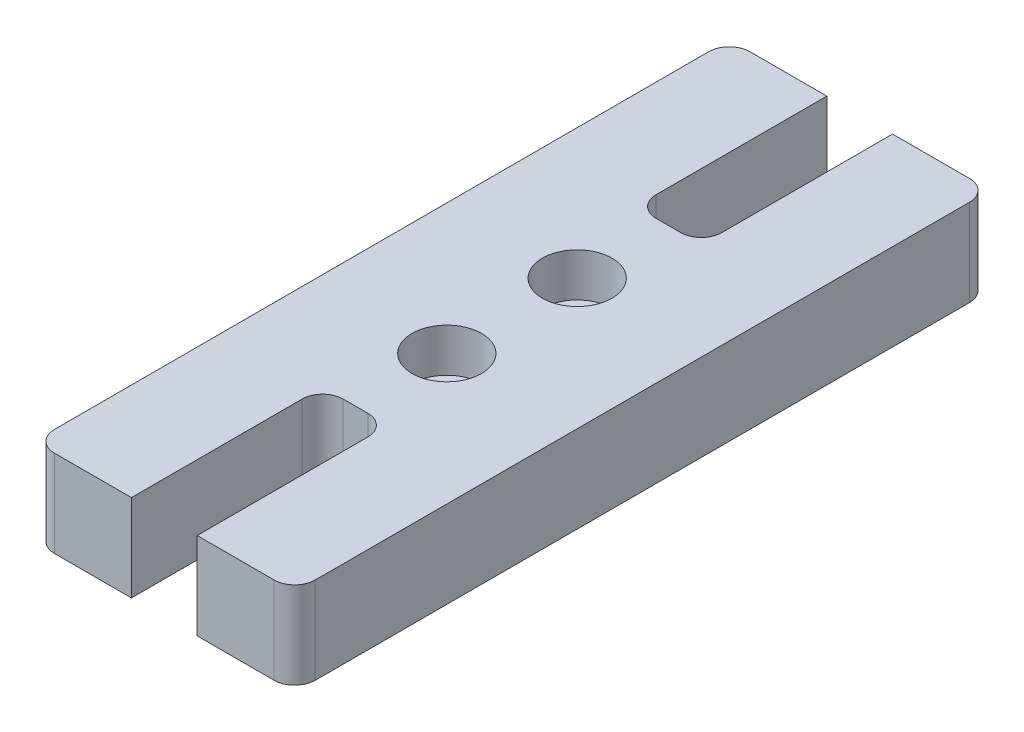
SolidWorks part; units mm, degrees
ref_plane "Front Plane" through (0, 0, 0) normal (0, 0, 1) x (1, 0, 0)
ref_plane "Top Plane" through (0, 0, 0) normal (0, 1, 0) x (1, 0, 0)
ref_plane "Right Plane" through (0, 0, 0) normal (1, 0, 0) x (0, 0, -1)
sketch "Sketch1" plane through (0, 0, 0) normal (0, 1, 0) x (1, 0, 0)
  line L1 (-9.525, -25.4) -> (9.525, -25.4)
  line L2 (-9.525, -25.4) -> (-9.525, 25.4)
  line L3 (-9.525, 25.4) -> (9.525, 25.4)
  line L4 (9.525, -25.4) -> (9.525, 25.4)
  line L5 (-9.525, -25.4) -> (9.525, 25.4) construction
  line L6 (-9.525, 25.4) -> (9.525, -25.4) construction
  point P0 (0, 0)
  dimension "D1" = 50.8
  dimension "D2" = 19.05
extrude "Boss-Extrude1" add sketch "Sketch1" along normal blind 6.35
sketch "Sketch2" plane through (0, 6.35, 0) normal (0, 1, 0) x (1, 0, 0)
  circle A0 centre (0, 4.7625) radius 1.7272
  dimension "D1" = 4.7625
  dimension "D2" = 3.4544
extrude "Cut-Extrude1" cut sketch "Sketch2" against normal through all and the other way through all
sketch "Sketch3" plane through (0, 6.35, 0) normal (0, 1, 0) x (1, 0, 0)
  circle A0 centre (0, 4.7625) radius 2.54
  dimension "D1" = 5.08
extrude "Cut-Extrude2" cut sketch "Sketch3" against normal blind 3.175
sketch "Sketch4" plane through (0, 6.35, 0) normal (0, 1, 0) x (1, 0, 0)
  line L0 (9.525, 25.4) -> (-9.525, 25.4) construction
  line L1 (-2.4003, 11.43) -> (2.4003, 11.43)
  line L2 (-2.4003, 11.43) -> (-2.4003, 25.4)
  line L3 (-2.4003, 25.4) -> (2.4003, 25.4)
  line L4 (2.4003, 11.43) -> (2.4003, 25.4)
  line L5 (-2.4003, 11.43) -> (2.4003, 25.4) construction
  line L6 (-2.4003, 25.4) -> (2.4003, 11.43) construction
  point P0 (0, 18.415)
  dimension "D1" = 4.8006
  dimension "D2" = 13.97
extrude "Cut-Extrude3" cut sketch "Sketch4" against normal through all
mirror "Mirror1" about plane through (0, 0, 0) normal (0, 0, 1) of "Cut-Extrude1", "Cut-Extrude2", "Cut-Extrude3"
fillet "Fillet2" radius 1.5 8 edges at (9.525, 3.175, 25.4) (-9.525, 3.175, 25.4) (2.4003, 3.175, 11.43) (-2.4003, 3.175, 11.43) (-2.4003, 3.175, -11.43) (2.4003, 3.175, -11.43) (9.525, 3.175, -25.4) (-9.525, 3.175, -25.4)
